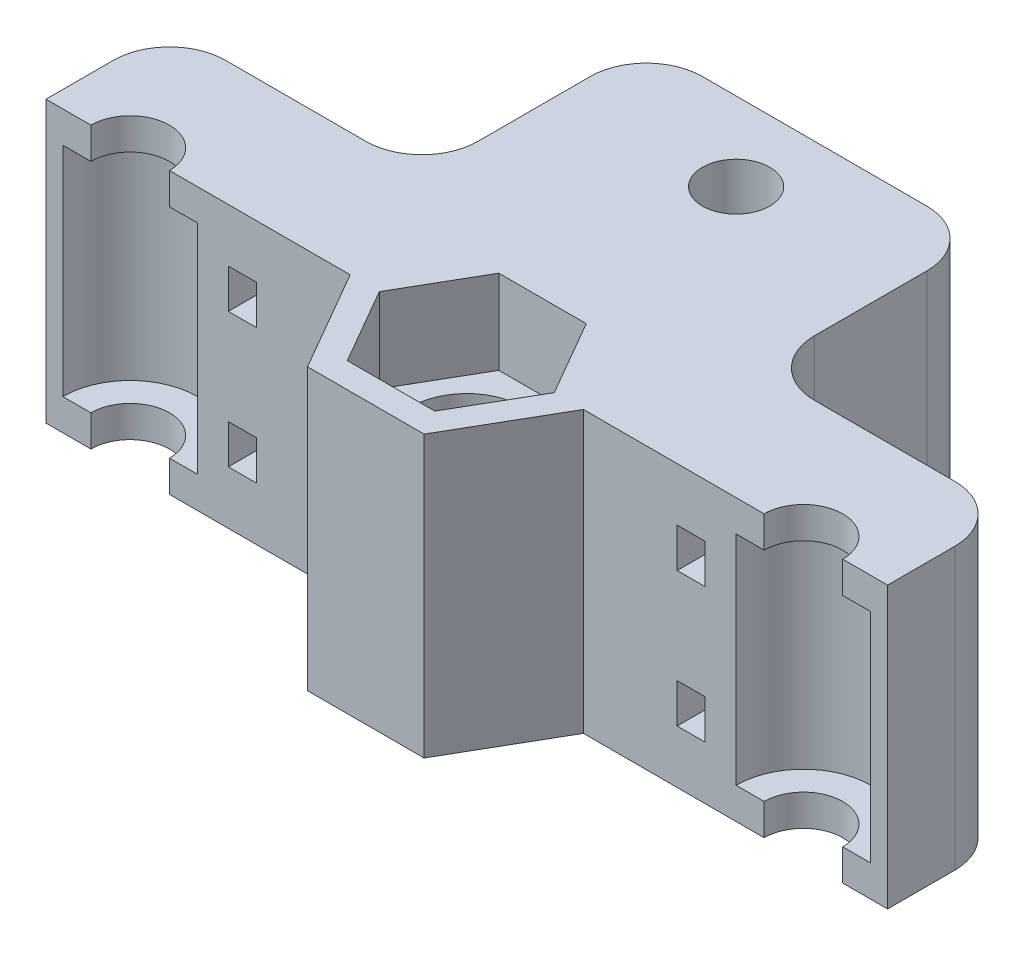
SolidWorks part; units mm, degrees
ref_plane "前基準面" through (0, 0, 0) normal (0, 0, 1) x (1, 0, 0)
ref_plane "上基準面" through (0, 0, 0) normal (0, 1, 0) x (1, 0, 0)
ref_plane "右基準面" through (0, 0, 0) normal (1, 0, 0) x (0, 0, -1)
sketch "草圖1" plane through (0, 0, 0) normal (0, 1, 0) x (1, 0, 0)
  line L0 (0, 33.1275) -> (0, -26.6057) construction
  line L1 (-37.5, 5.5) -> (-15, 5.5)
  line L2 (-37.5, 5.5) -> (-37.5, -5.5)
  line L3 (-37.5, -5.5) -> (-36, -5.5)
  line L4 (37.5, 5.5) -> (37.5, -5.5)
  line L5 (-6.6535, 0.9758) -> (37.5, -5.5) construction
  line L6 (-37.5, -5.5) -> (37.5, 5.5) construction
  line L7 (-15, 5.5) -> (-15, 25.5)
  line L8 (-15, 25.5) -> (15, 25.5)
  line L9 (15, 25.5) -> (15, 5.5)
  line L10 (15, 5.5) -> (37.5, 5.5)
  line L11 (-24, -5.5) -> (-10.3923, -5.5)
  line L12 (36, -5.5) -> (37.5, -5.5)
  line L13 (10.3923, -5.5) -> (24, -5.5)
  line L14 (3.8971, -12.25) -> (7.7942, -5.5)
  line L15 (7.7942, -5.5) -> (3.8971, 1.25)
  line L16 (3.8971, 1.25) -> (-3.8971, 1.25)
  line L17 (-3.8971, 1.25) -> (-7.7942, -5.5)
  line L18 (-7.7942, -5.5) -> (-3.8971, -12.25)
  line L19 (-3.8971, -12.25) -> (3.8971, -12.25)
  line L20 (7.8845, -1.1564) -> (7.7942, -1)
  line L22 (-7.7942, -1) -> (-7.8845, -1.1564)
  line L23 (-10.3923, -5.5) -> (-5.1962, -14.5)
  line L24 (-5.1962, -14.5) -> (5.1962, -14.5)
  line L25 (5.1962, -14.5) -> (10.3923, -5.5)
  line L26 (0, 3.5) -> (-5.1962, 3.5) [skipped]
  line L27 (-7.7942, -5.5) -> (7.7942, -5.5)
  arc A0 (-24, -5.5) -> (-36, -5.5) centre (-30, -5.5) ccw
  arc A1 (36, -5.5) -> (24, -5.5) centre (30, -5.5) ccw
  circle A2 centre (0, -5.5) radius 6.75 construction
  arc A3 (7.8823, -1.1561) -> (7.7942, -1) centre (0, -5.5) ccw construction
  arc A4 (-7.7942, -1) -> (-7.8823, -1.1561) centre (0, -5.5) ccw construction
  arc A5 (-7.7942, -10) -> (7.7942, -10) centre (0, -5.5) ccw construction
  point P0 (0, 0)
  dimension "D5" = 12
  dimension "D7" = 13.5
  dimension "D1" = 75
  dimension "D2" = 11
  dimension "D3" = 30
  dimension "D4" = 20
  dimension "D6" = 60
extrude "填料-伸長1" add sketch "草圖1" along normal mid plane 25
sketch "草圖2" plane through (0, 12.5, 0) normal (0, 1, 0) x (1, 0, 0)
  line L0 (0, 14.353) -> (0, -16.1566) construction
  line L1 (-36, -5.5) -> (-33.5, -5.5)
  line L2 (26.5, -5.5) -> (24, -5.5)
  line L3 (-26.5, -5.5) -> (-24, -5.5)
  line L4 (36, -5.5) -> (33.5, -5.5)
  arc A0 (-24, -5.5) -> (-36, -5.5) centre (-30, -5.5) ccw
  arc A1 (-26.5, -5.5) -> (-33.5, -5.5) centre (-30, -5.5) ccw
  arc A2 (26.5, -5.5) -> (33.5, -5.5) centre (30, -5.5) cw
  arc A3 (24, -5.5) -> (36, -5.5) centre (30, -5.5) cw
  dimension "D1" = 7
extrude "填料-伸長2" add sketch "草圖2" against normal blind 2.8
mirror "鏡射1" about plane through (0, 0, 0) normal (0, 1, 0) of "填料-伸長2"
sketch "草圖3" plane through (0, 0, 0) normal (0, 1, 0) x (1, 0, 0)
  line L1 (7.7942, -5.5) -> (3.8971, 1.25)
  line L2 (3.8971, 1.25) -> (-3.8971, 1.25)
  line L3 (-3.8971, 1.25) -> (-7.7942, -5.5)
  line L4 (-7.7942, -5.5) -> (-3.8971, -12.25)
  line L5 (-3.8971, -12.25) -> (3.8971, -12.25)
  line L6 (3.8971, -12.25) -> (7.7942, -5.5)
  circle A0 centre (0, -5.5) radius 6.75 construction
  circle A1 centre (0, -5.5) radius 5
  dimension "D1" = 10
extrude "填料-伸長3" add sketch "草圖3" along normal mid plane 10
fillet "圓角1" radius 5 6 edges at (-15, 0, -5.5) (-37.5, 0, -5.5) (37.5, 0, -5.5) (-15, 0, -25.5) (15, 0, -25.5) (15, 0, -5.5)
sketch "草圖4" plane through (0, 0, 5.5) normal (0, 0, 1) x (1, 0, 0)
  line L0 (0, 17.9423) -> (0, -22.4897) construction
  line L1 (-48.0438, 0) -> (42.0136, 0) construction
  line L2 (20, 21.9158) -> (20, -22.4897) construction
  line L3 (20, -22.4897) -> (-22.2425, -22.4897) construction
  line L4 (-22.2425, -22.4897) -> (-22.2425, 23.2805) construction
  line L5 (18.75, -4.25) -> (21.25, -7.75) construction
  line L6 (18.75, 7.75) -> (21.25, 7.75)
  line L7 (18.75, 7.75) -> (18.75, 4.25)
  line L8 (18.75, 4.25) -> (21.25, 4.25)
  line L9 (21.25, 7.75) -> (21.25, 4.25)
  line L10 (18.75, 7.75) -> (21.25, 4.25) construction
  line L11 (18.75, 4.25) -> (21.25, 7.75) construction
  line L12 (18.75, -7.75) -> (21.25, -4.25) construction
  line L13 (21.25, -7.75) -> (21.25, -4.25)
  line L14 (18.75, -4.25) -> (21.25, -4.25)
  line L15 (18.75, -7.75) -> (18.75, -4.25)
  line L16 (18.75, -7.75) -> (21.25, -7.75)
  line L17 (-18.75, -7.75) -> (-21.25, -4.25) construction
  line L18 (-18.75, 4.25) -> (-21.25, 7.75) construction
  line L19 (-18.75, 7.75) -> (-21.25, 4.25) construction
  line L20 (-18.75, -4.25) -> (-21.25, -7.75) construction
  line L21 (-18.75, -7.75) -> (-21.25, -7.75)
  line L22 (-18.75, -7.75) -> (-18.75, -4.25)
  line L23 (-18.75, -4.25) -> (-21.25, -4.25)
  line L24 (-21.25, -7.75) -> (-21.25, -4.25)
  line L25 (-21.25, 7.75) -> (-21.25, 4.25)
  line L26 (-18.75, 4.25) -> (-21.25, 4.25)
  line L27 (-18.75, 7.75) -> (-18.75, 4.25)
  line L28 (-18.75, 7.75) -> (-21.25, 7.75)
  point P7 (20, 6)
  point P18 (20, -6)
  point P27 (-20, -6)
  point P28 (-20, 6)
  dimension "D1" = 20
  dimension "D2" = 2.5
  dimension "D3" = 3.5
  dimension "D4" = 6
extrude "除料-伸長1" cut sketch "草圖4" against normal through all
sketch "草圖5" plane through (0, 12.5, 0) normal (0, 1, 0) x (1, 0, 0)
  circle A0 centre (0, 18.5) radius 3
  arc A1 (-26.5, -5.5) -> (-33.5, -5.5) centre (-30, -5.5) ccw construction
  dimension "D1" = 24
  dimension "D2" = 6
extrude "除料-伸長2" cut sketch "草圖5" against normal blind 5
